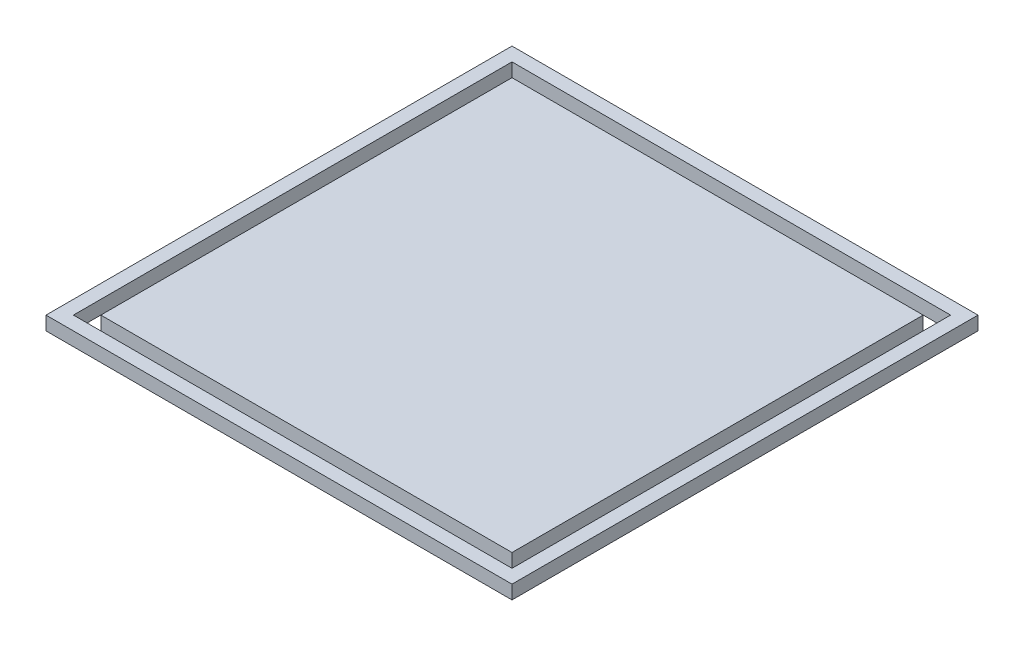
SolidWorks part; units mm, degrees
ref_plane "Front Plane" through (0, 0, 0) normal (0, 0, 1) x (1, 0, 0)
ref_plane "Top Plane" through (0, 0, 0) normal (0, 1, 0) x (1, 0, 0)
ref_plane "Right Plane" through (0, 0, 0) normal (1, 0, 0) x (0, 0, -1)
sketch "Sketch1" plane through (0, 0, 0) normal (0, 1, 0) x (1, 0, 0)
  line L0 (0, -150) -> (0, 150)
  line L1 (-150, 0) -> (150, 0)
  line L2 (-150, 0) -> (-150, 150)
  line L3 (-150, 150) -> (150, 150)
  line L4 (150, 150) -> (150, -150)
  line L5 (150, -150) -> (-150, -150)
  line L6 (-150, -150) -> (-150, 0)
  line L7 (-160, 0) -> (-160, 160)
  line L8 (-160, 160) -> (160, 160)
  line L9 (160, 160) -> (160, -160)
  line L10 (160, -160) -> (-160, -160)
  line L11 (-160, -160) -> (-160, 0)
  line L12 (-170, -170) -> (-170, 0)
  line L13 (-170, 0) -> (-170, 170)
  line L14 (-170, 170) -> (170, 170)
  line L15 (170, 170) -> (170, -170)
  line L16 (170, -170) -> (-170, -170)
  point P6 (0, 0)
  dimension "D1" = 10
  dimension "D2" = 10
extrude "Boss-Extrude1" add sketch "Sketch1" along normal blind 10 contours L16 L15 L14 L13 L12 L10 L11 L7 L8 L9 | L6 L5 L0 L1 | L3 L2 L1 L0 | L4 L3 L0 L1 | L5 L4 L1 L0
